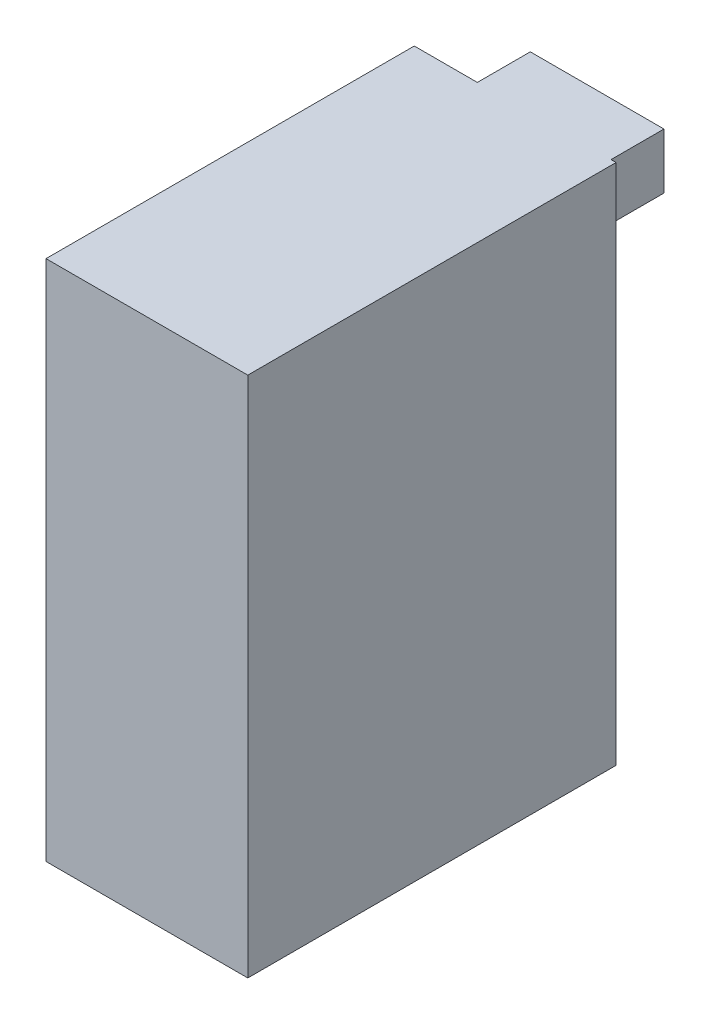
SolidWorks part; units mm, degrees
ref_plane "前视基准面" through (0, 0, 0) normal (0, 0, 1) x (1, 0, 0)
ref_plane "上视基准面" through (0, 0, 0) normal (0, 1, 0) x (1, 0, 0)
ref_plane "右视基准面" through (0, 0, 0) normal (1, 0, 0) x (0, 0, -1)
other "质心 (COM)"
sketch "草图1" plane through (0, 0, 0) normal (0, 1, 0) x (1, 0, 0)
  line L1 (-20, -36.5) -> (20, -36.5)
  line L2 (-20, -36.5) -> (-20, 36.5)
  line L3 (-20, 36.5) -> (20, 36.5)
  line L4 (20, -36.5) -> (20, 36.5)
  line L5 (-20, -36.5) -> (20, 36.5) construction
  line L6 (-20, 36.5) -> (20, -36.5) construction
  point P0 (0, 0)
  dimension "D1" = 40
  dimension "D2" = 73
extrude "凸台-拉伸1" add sketch "草图1" along normal mid plane 103.5
sketch "草图2" plane through (0, 0, -36.5) normal (0, 0, -1) x (-1, 0, 0)
  line L0 (-20, 51.75) -> (-20, -51.75) construction
  line L1 (-19, 51.75) -> (7.5, 51.75)
  line L2 (-19, 51.75) -> (-19, 40.75)
  line L3 (-19, 40.75) -> (7.5, 40.75)
  line L4 (7.5, 51.75) -> (7.5, 40.75)
  dimension "D1" = 11
  dimension "D2" = 26.5
  dimension "D3" = 1
extrude "凸台-拉伸2" add sketch "草图2" along normal blind 10.5
sketch "草图3" plane through (0, 0, -47) normal (0, 0, -1) x (-1, 0, 0)
  line L0 (-30, 51.75) -> (30, 51.75)
  line L2 (-20, -51.75) -> (20, -51.75) construction
  spline S0 degree 3 poles (-30, 51.75) (-32.9608, 67.553) (-0.1223, 116.2579) (33.0721, 64.9367) (30, 51.75) knots 0 0 0 0 0.500505 1 1 1 1
  point P4 (0, 51.75)
  point P12 (-16.8524, 83.8663)
  dimension "D1" = 60
  dimension "D2" = 143
sketch "草图4" plane through (0, 0, 36.5) normal (0, 0, 1) x (1, 0, 0)
  line L0 (-26, 51.75) -> (26, 51.75)
  line L1 (30, 51.75) -> (-30, 51.75) construction
  arc A0 (-26, 51.75) -> (26, 51.75) centre (0, 36.1214) cw
  point P4 (0, 51.75)
  dimension "D1" = 52
loft "放样1" add profiles "草图3", "草图4"
sketch "草图5" plane through (0, 51.75, 0) normal (0, -1, 0) x (1, 0, 0)
  line L0 (0, 13.4118) -> (0, -19.6269) construction
  line L1 (-27.3413, 8.5) -> (-26.243, 8.5)
  line L3 (-22.243, 4.5) -> (-22.243, -30.5)
  line L4 (-26.243, -34.5) -> (-29.4012, -34.5)
  line L5 (-29.4012, -34.5) -> (-36.9893, -34.5)
  line L6 (-26, 36.5) -> (26, 36.5) construction
  line L7 (36.9893, 9.3475) -> (27.3413, 8.5)
  line L8 (36.9893, -34.5) -> (36.9893, 9.3475)
  line L9 (29.4012, -34.5) -> (36.9893, -34.5)
  line L10 (26.243, -34.5) -> (29.4012, -34.5)
  line L12 (-36.9893, -34.5) -> (-36.9893, 9.3475)
  line L13 (-36.9893, 9.3475) -> (-27.3413, 8.5)
  line L14 (22.243, 4.5) -> (22.243, -30.5)
  line L15 (27.3413, 8.5) -> (26.243, 8.5)
  arc A0 (-22.243, -30.5) -> (-26.243, -34.5) centre (-26.243, -30.5) cw
  arc A1 (-22.243, 4.5) -> (-26.243, 8.5) centre (-26.243, 4.5) ccw
  arc A2 (22.243, 4.5) -> (26.243, 8.5) centre (26.243, 4.5) cw
  arc A3 (22.243, -30.5) -> (26.243, -34.5) centre (26.243, -30.5) ccw
  dimension "D3" = 4
  dimension "D1" = 28
  dimension "D2" = 71
extrude "切除-拉伸1" cut sketch "草图5" against normal through all
sketch "草图6" plane through (0, 0, -47) normal (0, 0, -1) x (-1, 0, 0)
  line L1 (34.9879, 51.75) -> (-35.2914, 51.75)
  line L2 (34.9879, 51.75) -> (34.9879, 100.8033)
  line L3 (34.9879, 100.8033) -> (-35.2914, 100.8033)
  line L4 (-35.2914, 51.75) -> (-35.2914, 100.8033)
extrude "切除-拉伸2" cut sketch "草图6" against normal through all
